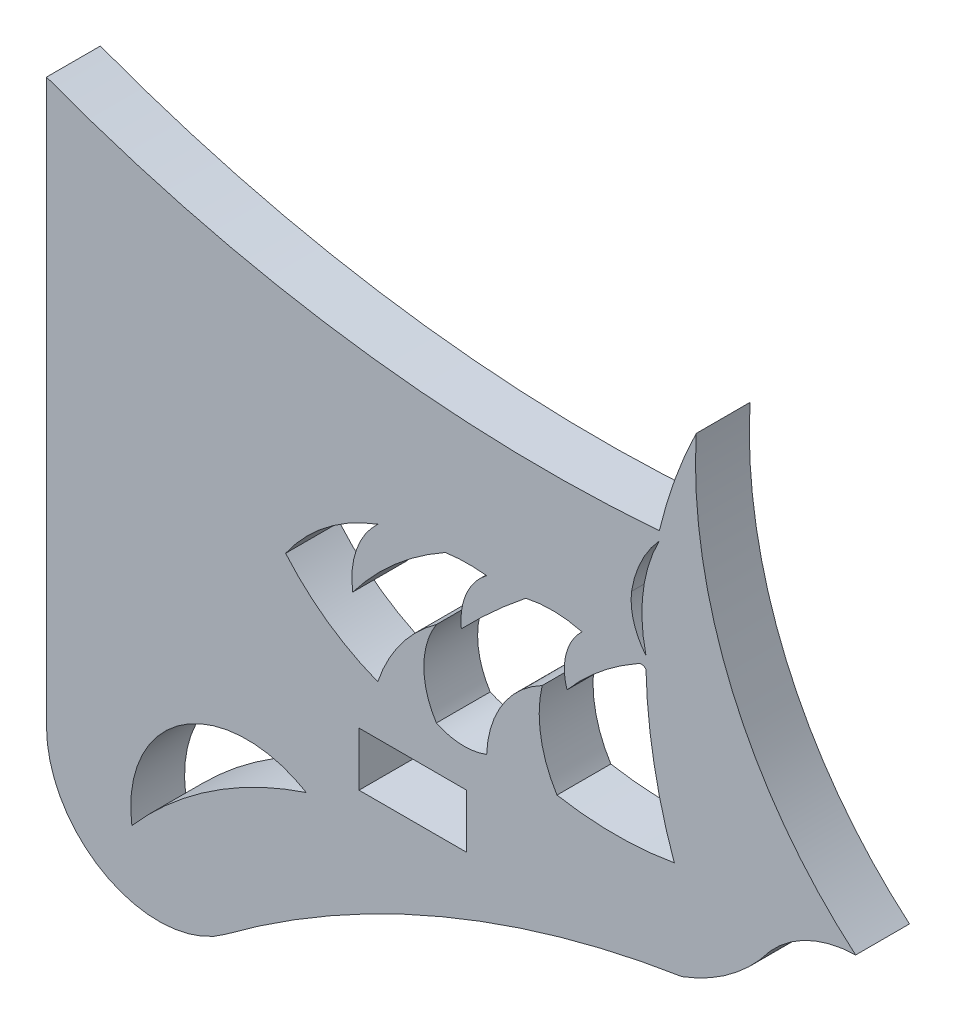
SolidWorks part; units mm, degrees
ref_plane "Front Plane" through (0, 0, 0) normal (0, 0, 1) x (1, 0, 0)
ref_plane "Top Plane" through (0, 0, 0) normal (0, 1, 0) x (1, 0, 0)
ref_plane "Right Plane" through (0, 0, 0) normal (1, 0, 0) x (0, 0, -1)
sketch "Sketch1" plane through (0, 0, 0) normal (0, 0, 1) x (1, 0, 0)
  line L0 (18.812, -1.524) -> (12.5784, -1.524) construction
  line L1 (0.6802, -6.1294) -> (0.6802, 11.5407)
  line L2 (12.5784, -1.524) -> (9.5304, -1.524)
  line L3 (12.5784, -1.524) -> (12.5784, 0)
  line L4 (12.5784, 0) -> (9.5304, 0)
  line L5 (9.5304, -1.524) -> (9.5304, 0)
  arc A0 (21.1693, 0.3458) -> (18.6754, -1.524) centre (16.7553, 3.6351) cw
  arc A1 (18.6754, -1.524) -> (3.7115, -8.6105) centre (23.2022, -30.4251) ccw
  arc A2 (3.7115, -8.6105) -> (0.6802, -6.1294) centre (3.096, -6.2702) cw
  arc A3 (21.1693, 0.3458) -> (23.5942, 1.4658) centre (23.6638, -1.8699) cw
  arc A4 (23.5942, 1.4658) -> (19.0795, 12.0014) centre (31.9114, 11.2649) cw
  arc A5 (19.0795, 12.0014) -> (18.0345, 9.0914) centre (31.6627, 5.8401) ccw
  arc A6 (18.4572, 1.159) -> (15.136, 1.159) centre (16.7966, 10.4704) cw
  arc A7 (15.136, 1.159) -> (14.7153, 3.6351) centre (17.899, 2.9022) cw
  arc A8 (14.7153, 3.6351) -> (13.1443, 1.159) centre (16.044, 1.0557) ccw
  arc A9 (13.1443, 1.159) -> (11.7205, 1.2194) centre (12.5028, 2.8509) cw
  arc A10 (11.7205, 1.2194) -> (11.7205, 3.6351) centre (13.5926, 2.4272) cw
  arc A11 (11.7205, 3.6351) -> (10.0612, 1.4008) centre (14.2969, -0.0115) ccw
  arc A12 (10.0612, 1.4008) -> (7.4502, 3.2457) centre (12.4021, 7.4838) cw
  arc A13 (7.4502, 3.2457) -> (10.0612, 5.2641) centre (11.9717, 0.0944) cw
  arc A14 (10.0612, 5.2641) -> (9.3524, 3.2457) centre (11.6268, 3.5806) ccw
  arc A15 (9.3524, 3.2457) -> (11.9717, 5.5267) centre (16.0846, -1.8406) cw
  arc A16 (11.9717, 5.5267) -> (13.1443, 5.5454) centre (12.6308, 0.965) cw
  arc A17 (13.1443, 5.5454) -> (12.4262, 3.8816) centre (14.2538, 4.0797) ccw
  arc A18 (12.4262, 3.8816) -> (14.2538, 5.5454) centre (25.899, -9.0817) cw
  arc A19 (14.2538, 5.5454) -> (15.8462, 5.5166) centre (14.9905, 2.2378) cw
  arc A20 (15.8462, 5.5166) -> (15.4195, 3.8816) centre (16.9256, 4.3617) ccw
  arc A21 (15.4195, 3.8816) -> (17.4043, 5.5166) centre (21.0707, -0.9564) cw
  arc A22 (17.4043, 5.5166) -> (17.6561, 5.5048) centre (17.5244, 5.3866) cw
  arc A23 (18.0345, 9.0914) -> (0.6802, 11.5407) centre (14.856, 49.2765) cw
  arc A24 (17.6561, 5.5048) -> (18.4572, 1.159) centre (31.6627, 5.8401) ccw
  arc A25 (17.6561, 5.8401) -> (18.0345, 8.8421) centre (21.8721, 6.8335) cw
  arc A26 (18.0345, 8.8421) -> (17.2467, 7.2113) centre (20.3635, 6.7113) ccw
  arc A27 (17.2467, 7.2113) -> (17.6561, 5.8401) centre (19.0664, 7.0079) ccw
  arc A28 (8.0375, -2.3276) -> (3.096, -5.6078) centre (11.581, -13.0278) ccw
  arc A29 (3.096, -5.6078) -> (8.0375, -2.3276) centre (6.356, -5.1567) cw
extrude "Boss-Extrude1" add sketch "Sketch1" along normal blind 1.524
fillet "Fillet4" radius 3.175 1 edges at (3.7115, -8.6105, 0.762)
